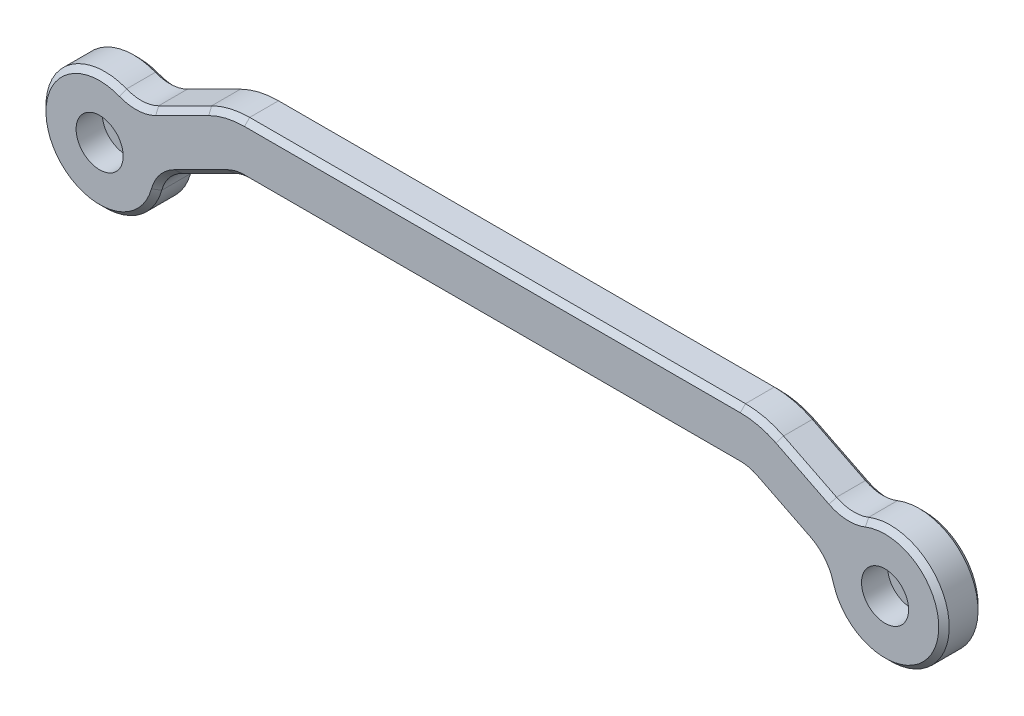
SolidWorks part; units mm, degrees
ref_plane "Front Plane" through (0, 0, 0) normal (0, 0, 1) x (1, 0, 0)
ref_plane "Top Plane" through (0, 0, 0) normal (0, 1, 0) x (1, 0, 0)
ref_plane "Right Plane" through (0, 0, 0) normal (1, 0, 0) x (0, 0, -1)
sketch "Sketch1" plane through (0, 0, 0) normal (0, 0, 1) x (1, 0, 0)
  line L0 (-60, 0) -> (60, 0) construction
  line L1 (-60, 0) -> (-40, 10) construction
  line L2 (-40, 10) -> (40, 10) construction
  line L3 (40, 10) -> (60, 0) construction
  line L4 (-40.9443, 14) -> (40.9443, 14) construction
  line L5 (40.9443, 14) -> (61.7889, 3.5777) construction
  line L6 (-61.7889, 3.5777) -> (-40.9443, 14) construction
  line L7 (-51.7889, 8.5777) -> (-43.6892, 12.6276)
  line L8 (-37.8754, 14) -> (37.8754, 14)
  line L9 (43.6892, 12.6276) -> (51.7889, 8.5777)
  line L10 (43.6892, 12.6276) -> (61.7889, 3.5777) construction
  line L11 (-37.8754, 6) -> (37.8754, 6)
  line L12 (40.1115, 5.4721) -> (48.2111, 1.4223)
  line L13 (-61.7889, 3.5777) -> (-43.6892, 12.6276) construction
  line L14 (-48.2111, 1.4223) -> (-40.1115, 5.4721)
  line L15 (-58.2111, -3.5777) -> (-40.1115, 5.4721) construction
  line L17 (40.1115, 5.4721) -> (58.2111, -3.5777) construction
  circle A0 centre (-60, 0) radius 2.05
  circle A1 centre (60, 0) radius 2.05
  arc A2 (-56.6833, 8.3666) -> (-51.3167, -2.3666) centre (-60, 0) ccw
  arc A3 (51.3167, -2.3666) -> (56.6833, 8.3666) centre (60, 0) ccw
  arc A4 (37.8754, 14) -> (43.6892, 12.6276) centre (37.8754, 1) cw
  arc A5 (-43.6892, 12.6276) -> (-37.8754, 14) centre (-37.8754, 1) cw
  arc A6 (-40.1115, 5.4721) -> (-37.8754, 6) centre (-37.8754, 1) cw
  arc A7 (37.8754, 6) -> (40.1115, 5.4721) centre (37.8754, 1) cw
  arc A8 (-51.7889, 8.5777) -> (-56.6833, 8.3666) centre (-54.4721, 13.9443) cw
  arc A9 (51.7889, 8.5777) -> (56.6833, 8.3666) centre (54.4721, 13.9443) ccw
  arc A10 (48.2111, 1.4223) -> (51.3167, -2.3666) centre (45.5279, -3.9443) cw
  arc A11 (-51.3167, -2.3666) -> (-48.2111, 1.4223) centre (-45.5279, -3.9443) cw
  point P4 (0, 0)
  point P9 (0, 10)
  dimension "D1" = 4.1
  dimension "D2" = 4.1
  dimension "D3" = 18
  dimension "D4" = 18
  dimension "D8" = 13
  dimension "D11" = 6
  dimension "D12" = 8
  dimension "D10" = 6
  dimension "D5" = 120
  dimension "D6" = 80
  dimension "D7" = 10
  dimension "D9" = 4
extrude "Boss-Extrude1" add sketch "Sketch1" along normal blind 6
sketch "Sketch3" plane through (0, 0, 6) normal (0, 0, 1) x (1, 0, 0)
  circle A0 centre (-60, 0) radius 3.6
  circle A1 centre (60, 0) radius 3.6
  dimension "D1" = 7.2
extrude "Cut-Extrude1" cut sketch "Sketch3" against normal blind 4
chamfer "Chamfer3" distance 0.8 angle 45 32 edges at (39.0242, 5.8662, 0) (44.1613, 3.4472, 0) (0, 6, 0) (50.1682, -0.1407, 0) (-39.0242, 5.8662, 0) (68.0498, -4.0249, 0) (-44.1613, 3.4472, 0) (54.2135, 7.9498, 0) (-50.1682, -0.1407, 0) (47.739, 10.6026, 0) (-68.0498, -4.0249, 0) (40.8622, 13.6522, 0) (-54.2135, 7.9498, 0) (0, 14, 0) (-47.739, 10.6026, 0) (-40.8622, 13.6522, 0) (39.0242, 5.8662, 6) (44.1613, 3.4472, 6) (0, 6, 6) (50.1682, -0.1407, 6) (-39.0242, 5.8662, 6) (68.0498, -4.0249, 6) (-44.1613, 3.4472, 6) (54.2135, 7.9498, 6) (-50.1682, -0.1407, 6) (47.739, 10.6026, 6) (-68.0498, -4.0249, 6) (40.8622, 13.6522, 6) (-54.2135, 7.9498, 6) (0, 14, 6) (-47.739, 10.6026, 6) (-40.8622, 13.6522, 6)
